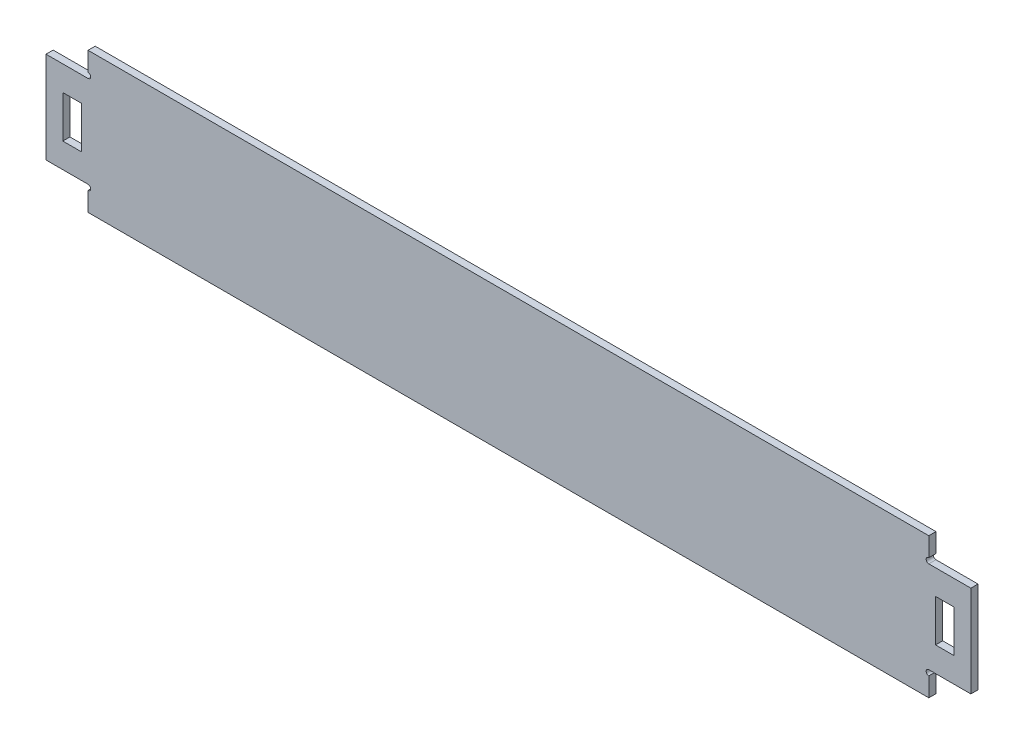
SolidWorks part; units mm, degrees
material "Teak"
ref_plane "Front Plane" through (0, 0, 0) normal (0, 0, 1) x (1, 0, 0)
ref_plane "Top Plane" through (0, 0, 0) normal (0, 1, 0) x (1, 0, 0)
ref_plane "Right Plane" through (0, 0, 0) normal (1, 0, 0) x (0, 0, -1)
sketch "Sketch1" plane through (0, 0, 0) normal (0, 0, 1) x (1, 0, 0)
  line L0 (1.4307, -82.0313) -> (1.4307, 84.9687) construction
  line L1 (-498.5693, 84.9687) -> (501.4307, 84.9687)
  line L2 (-498.5693, 84.9687) -> (-498.5693, 62.3287)
  line L3 (-498.5693, -82.0313) -> (501.4307, -82.0313)
  line L4 (501.4307, 84.9687) -> (501.4307, 62.3287)
  line L5 (-498.5693, 84.9687) -> (501.4307, -82.0313) construction
  line L6 (-498.5693, -82.0313) -> (501.4307, 84.9687) construction
  line L7 (-998.5693, 1.4687) -> (49001.4307, 1.4687) construction
  line L8 (509.4307, 26.4687) -> (509.4307, -23.5313)
  line L9 (-548.5693, 55.9687) -> (-498.5693, 55.9687)
  line L10 (-548.5693, 55.9687) -> (-548.5693, -53.0313)
  line L11 (-548.5693, -53.0313) -> (-498.5693, -53.0313)
  line L12 (-498.5693, 55.9687) -> (-498.5693, -53.0313)
  line L13 (-528.5693, 26.4687) -> (-506.5693, 26.4687)
  line L14 (-528.5693, 26.4687) -> (-528.5693, -23.5313)
  line L15 (-528.5693, -23.5313) -> (-506.5693, -23.5313)
  line L16 (-506.5693, 26.4687) -> (-506.5693, -23.5313)
  line L17 (531.4307, -23.5313) -> (509.4307, -23.5313)
  line L18 (531.4307, 26.4687) -> (531.4307, -23.5313)
  line L19 (531.4307, 26.4687) -> (509.4307, 26.4687)
  line L20 (551.4307, -53.0313) -> (501.4307, -53.0313)
  line L21 (551.4307, 55.9687) -> (551.4307, -53.0313)
  line L22 (551.4307, 55.9687) -> (501.4307, 55.9687)
  line L23 (501.4307, 55.9687) -> (501.4307, -53.0313)
  line L24 (501.4307, -59.3913) -> (501.4307, -82.0313)
  line L25 (-498.5693, -59.3913) -> (-498.5693, -82.0313)
  line L26 (-498.5693, 55.9687) -> (-498.5693, -53.0313)
  arc A0 (501.4307, 55.9687) -> (501.4307, 62.3287) centre (501.4307, 59.1487) cw
  arc A1 (501.4307, -53.0313) -> (501.4307, -59.3913) centre (501.4307, -56.2113) ccw
  arc A2 (-498.5693, 55.9687) -> (-498.5693, 62.3287) centre (-498.5693, 59.1487) ccw
  arc A3 (-498.5693, -53.0313) -> (-498.5693, -59.3913) centre (-498.5693, -56.2113) cw
  point P0 (1.4307, 1.4687)
  point P13 (-548.5693, 1.4687)
  point P18 (-528.5693, 1.4687)
  dimension "D8" = 3.18
  dimension "D1" = 1000
  dimension "D2" = 167
  dimension "D3" = 50
  dimension "D4" = 109
  dimension "D5" = 20
  dimension "D6" = 8
  dimension "D7" = 50
extrude "Boss-Extrude1" add sketch "Sketch1" along normal mid plane 8.5 contours L4 L1 L2 L3 | L10 L11 L2 L9 L13 L16 L15 L14 | L21 L22 L4 L20 L19 L18 L17 L8
